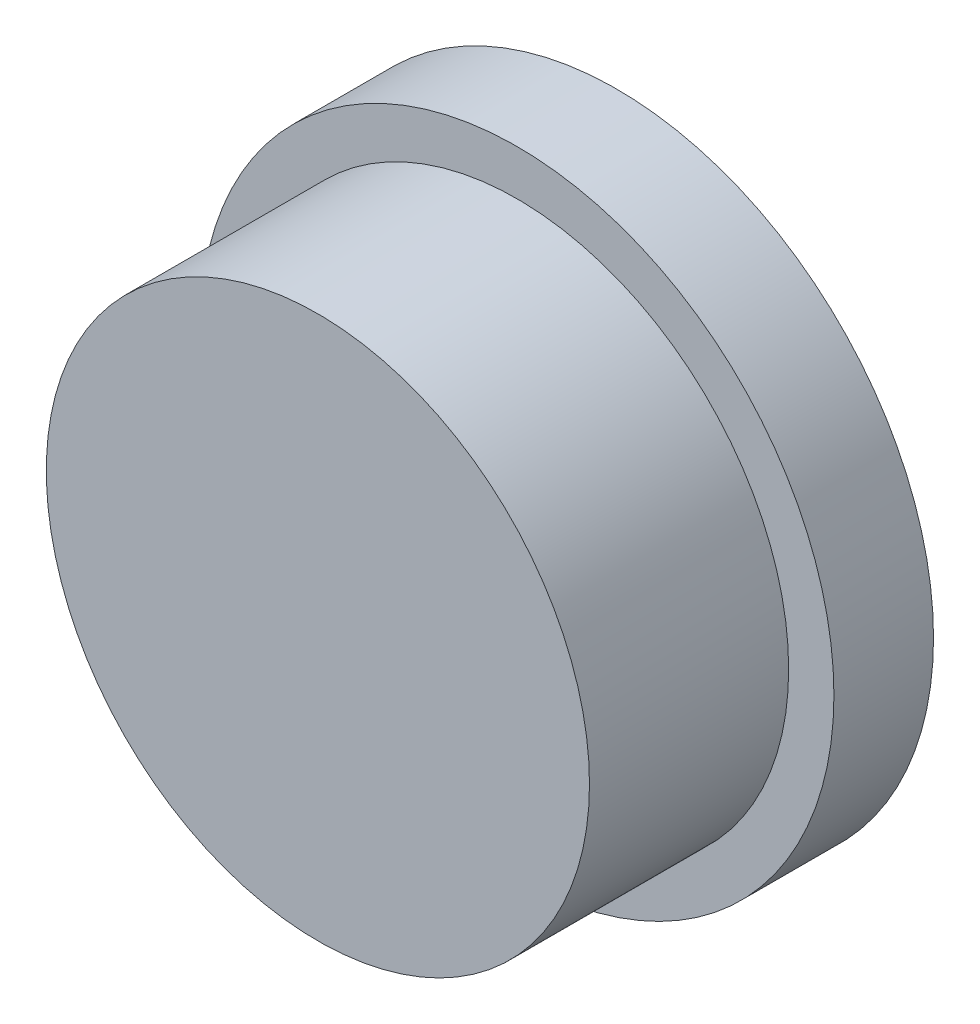
SolidWorks part; units mm, degrees
ref_plane "Alzado" through (0, 0, 0) normal (0, 0, 1) x (1, 0, 0)
ref_plane "Planta" through (0, 0, 0) normal (0, 1, 0) x (1, 0, 0)
ref_plane "Vista lateral" through (0, 0, 0) normal (1, 0, 0) x (0, 0, -1)
sketch "Croquis2" plane through (0, 0, 0) normal (0, 0, 1) x (1, 0, 0)
  circle A0 centre (0, 0) radius 35
  circle A1 centre (0, 0) radius 30
  dimension "D1" = 70
  dimension "D2" = 60
extrude "Saliente-Extruir1" add sketch "Croquis2" along normal blind 11
sketch "Croquis5" plane through (0, 0, 11) normal (0, 0, 1) x (1, 0, 0)
  circle A0 centre (0, 0) radius 30
extrude "Saliente-Extruir3" add sketch "Croquis5" along normal blind 22 separate body
